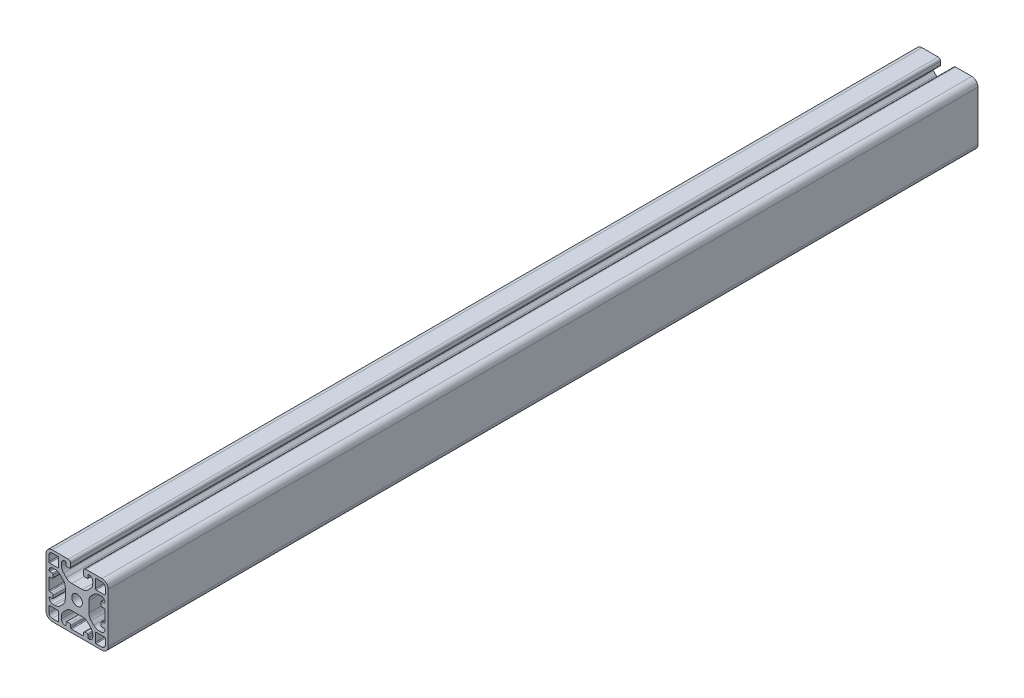
SolidWorks part; units mm, degrees
ref_plane "Ebene vorne" through (0, 0, 0) normal (0, 0, 1) x (1, 0, 0)
ref_plane "Ebene oben" through (0, 0, 0) normal (0, 1, 0) x (1, 0, 0)
ref_plane "Ebene rechts" through (0, 0, 0) normal (1, 0, 0) x (0, 0, -1)
ref_plane "Ebene1" through (0, 0, 560) normal (0, 0, 1) x (1, 0, 0)
sketch "Skizze1" plane through (0, 0, 560) normal (0, 0, 1) x (1, 0, 0)
  line L0 (0, 38.2) -> (3.7, 38.2)
  line L1 (4.2, 37.7) -> (4.2, 32.3)
  line L2 (3.7, 31.8) -> (-1.7, 31.8)
  line L3 (-2.2, 32.3) -> (-2.2, 36)
  line L4 (-2.2, 4) -> (-2.2, 7.7)
  line L5 (-1.7, 8.2) -> (3.7, 8.2)
  line L6 (4.2, 7.7) -> (4.2, 2.3)
  line L7 (3.7, 1.8) -> (0, 1.8)
  line L8 (32, 1.8) -> (28.3, 1.8)
  line L9 (27.8, 2.3) -> (27.8, 7.7)
  line L10 (28.3, 8.2) -> (33.7, 8.2)
  line L11 (34.2, 7.7) -> (34.2, 4)
  line L12 (34.2, 36) -> (34.2, 32.3)
  line L13 (33.7, 31.8) -> (28.3, 31.8)
  line L14 (27.8, 32.3) -> (27.8, 37.7)
  line L15 (28.3, 38.2) -> (32, 38.2)
  line L16 (12.5924, 12.4) -> (19.4076, 12.4)
  line L17 (22.9431, 10.9355) -> (24.6355, 9.2431)
  line L18 (26.1, 5.7076) -> (26.1, 4.5)
  line L19 (23.1, 2.5) -> (23.1, 4.15)
  line L20 (22.6, 4.65) -> (21.1, 4.65)
  line L21 (20.1, 3.65) -> (20.1, 2.5)
  line L22 (19.6, 2) -> (12.4, 2)
  line L23 (11.9, 2.5) -> (11.9, 3.65)
  line L24 (10.9, 4.65) -> (9.4, 4.65)
  line L25 (8.9, 4.15) -> (8.9, 2.5)
  line L26 (5.9, 4.5) -> (5.9, 5.7076)
  line L27 (7.3645, 9.2431) -> (9.0569, 10.9355)
  line L28 (-0.35, 15.9) -> (-1.5, 15.9)
  line L29 (-2, 16.4) -> (-2, 23.6)
  line L30 (-1.5, 24.1) -> (-0.35, 24.1)
  line L31 (0.65, 25.1) -> (0.65, 26.6)
  line L32 (0.15, 27.1) -> (-1.5, 27.1)
  line L33 (0.5, 30.1) -> (1.7076, 30.1)
  line L34 (5.2431, 28.6355) -> (6.9355, 26.9431)
  line L35 (8.4, 23.4076) -> (8.4, 16.5924)
  line L36 (6.9355, 13.0569) -> (5.2431, 11.3645)
  line L37 (1.7076, 9.9) -> (0.5, 9.9)
  line L38 (-1.5, 12.9) -> (0.15, 12.9)
  line L39 (0.65, 13.4) -> (0.65, 14.9)
  line L40 (23.6, 16.5924) -> (23.6, 23.4076)
  line L41 (25.0645, 26.9431) -> (26.7569, 28.6355)
  line L42 (30.2924, 30.1) -> (31.5, 30.1)
  line L43 (33.5, 27.1) -> (31.85, 27.1)
  line L44 (31.35, 26.6) -> (31.35, 25.1)
  line L45 (32.35, 24.1) -> (33.5, 24.1)
  line L46 (34, 23.6) -> (34, 16.4)
  line L47 (33.5, 15.9) -> (32.35, 15.9)
  line L48 (31.35, 14.9) -> (31.35, 13.4)
  line L49 (31.85, 12.9) -> (33.5, 12.9)
  line L50 (31.5, 9.9) -> (30.2924, 9.9)
  line L51 (26.7569, 11.3645) -> (25.0645, 13.0569)
  line L52 (23.1, 35.85) -> (23.1, 37.5)
  line L53 (26.1, 35.5) -> (26.1, 34.2924)
  line L54 (24.6355, 30.7569) -> (22.9431, 29.0645)
  line L55 (19.4076, 27.6) -> (12.5924, 27.6)
  line L56 (9.0569, 29.0645) -> (7.3645, 30.7569)
  line L57 (5.9, 34.2924) -> (5.9, 35.5)
  line L58 (8.9, 37.5) -> (8.9, 35.85)
  line L59 (9.4, 35.35) -> (10.9, 35.35)
  line L60 (11.9, 36.35) -> (11.9, 38.5)
  line L61 (10.4, 40) -> (0, 40)
  line L62 (-4, 36) -> (-4, 4)
  line L63 (0, 0) -> (32, 0)
  line L64 (36, 4) -> (36, 36)
  line L65 (32, 40) -> (21.6, 40)
  line L66 (20.1, 38.5) -> (20.1, 36.35)
  line L67 (21.1, 35.35) -> (22.6, 35.35)
  circle A0 centre (16, 20) radius 3.4
  arc A1 (3.7, 38.2) -> (4.2, 37.7) centre (3.7, 37.7) cw
  arc A2 (4.2, 32.3) -> (3.7, 31.8) centre (3.7, 32.3) cw
  arc A3 (-1.7, 31.8) -> (-2.2, 32.3) centre (-1.7, 32.3) cw
  arc A4 (-2.2, 36) -> (0, 38.2) centre (0, 36) cw
  arc A5 (-2.2, 7.7) -> (-1.7, 8.2) centre (-1.7, 7.7) cw
  arc A6 (3.7, 8.2) -> (4.2, 7.7) centre (3.7, 7.7) cw
  arc A7 (4.2, 2.3) -> (3.7, 1.8) centre (3.7, 2.3) cw
  arc A8 (0, 1.8) -> (-2.2, 4) centre (0, 4) cw
  arc A9 (28.3, 1.8) -> (27.8, 2.3) centre (28.3, 2.3) cw
  arc A10 (27.8, 7.7) -> (28.3, 8.2) centre (28.3, 7.7) cw
  arc A11 (33.7, 8.2) -> (34.2, 7.7) centre (33.7, 7.7) cw
  arc A12 (34.2, 4) -> (32, 1.8) centre (32, 4) cw
  arc A13 (34.2, 32.3) -> (33.7, 31.8) centre (33.7, 32.3) cw
  arc A14 (28.3, 31.8) -> (27.8, 32.3) centre (28.3, 32.3) cw
  arc A15 (27.8, 37.7) -> (28.3, 38.2) centre (28.3, 37.7) cw
  arc A16 (32, 38.2) -> (34.2, 36) centre (32, 36) cw
  arc A17 (19.4076, 12.4) -> (22.9431, 10.9355) centre (19.4076, 7.4) cw
  arc A18 (24.6355, 9.2431) -> (26.1, 5.7076) centre (21.1, 5.7076) cw
  arc A19 (26.1, 4.5) -> (23.6, 2) centre (23.6, 4.5) cw
  arc A20 (23.6, 2) -> (23.1, 2.5) centre (23.6, 2.5) cw
  arc A21 (23.1, 4.15) -> (22.6, 4.65) centre (22.6, 4.15) ccw
  arc A22 (21.1, 4.65) -> (20.1, 3.65) centre (21.1, 3.65) ccw
  arc A23 (20.1, 2.5) -> (19.6, 2) centre (19.6, 2.5) cw
  arc A24 (12.4, 2) -> (11.9, 2.5) centre (12.4, 2.5) cw
  arc A25 (11.9, 3.65) -> (10.9, 4.65) centre (10.9, 3.65) ccw
  arc A26 (9.4, 4.65) -> (8.9, 4.15) centre (9.4, 4.15) ccw
  arc A27 (8.9, 2.5) -> (8.4, 2) centre (8.4, 2.5) cw
  arc A28 (8.4, 2) -> (5.9, 4.5) centre (8.4, 4.5) cw
  arc A29 (5.9, 5.7076) -> (7.3645, 9.2431) centre (10.9, 5.7076) cw
  arc A30 (9.0569, 10.9355) -> (12.5924, 12.4) centre (12.5924, 7.4) cw
  arc A31 (-1.5, 15.9) -> (-2, 16.4) centre (-1.5, 16.4) cw
  arc A32 (-2, 23.6) -> (-1.5, 24.1) centre (-1.5, 23.6) cw
  arc A33 (-0.35, 24.1) -> (0.65, 25.1) centre (-0.35, 25.1) ccw
  arc A34 (0.65, 26.6) -> (0.15, 27.1) centre (0.15, 26.6) ccw
  arc A35 (-1.5, 27.1) -> (-2, 27.6) centre (-1.5, 27.6) cw
  arc A36 (-2, 27.6) -> (0.5, 30.1) centre (0.5, 27.6) cw
  arc A37 (1.7076, 30.1) -> (5.2431, 28.6355) centre (1.7076, 25.1) cw
  arc A38 (6.9355, 26.9431) -> (8.4, 23.4076) centre (3.4, 23.4076) cw
  arc A39 (8.4, 16.5924) -> (6.9355, 13.0569) centre (3.4, 16.5924) cw
  arc A40 (5.2431, 11.3645) -> (1.7076, 9.9) centre (1.7076, 14.9) cw
  arc A41 (0.5, 9.9) -> (-2, 12.4) centre (0.5, 12.4) cw
  arc A42 (-2, 12.4) -> (-1.5, 12.9) centre (-1.5, 12.4) cw
  arc A43 (0.15, 12.9) -> (0.65, 13.4) centre (0.15, 13.4) ccw
  arc A44 (0.65, 14.9) -> (-0.35, 15.9) centre (-0.35, 14.9) ccw
  arc A45 (23.6, 23.4076) -> (25.0645, 26.9431) centre (28.6, 23.4076) cw
  arc A46 (26.7569, 28.6355) -> (30.2924, 30.1) centre (30.2924, 25.1) cw
  arc A47 (31.5, 30.1) -> (34, 27.6) centre (31.5, 27.6) cw
  arc A48 (34, 27.6) -> (33.5, 27.1) centre (33.5, 27.6) cw
  arc A49 (31.85, 27.1) -> (31.35, 26.6) centre (31.85, 26.6) ccw
  arc A50 (31.35, 25.1) -> (32.35, 24.1) centre (32.35, 25.1) ccw
  arc A51 (33.5, 24.1) -> (34, 23.6) centre (33.5, 23.6) cw
  arc A52 (34, 16.4) -> (33.5, 15.9) centre (33.5, 16.4) cw
  arc A53 (32.35, 15.9) -> (31.35, 14.9) centre (32.35, 14.9) ccw
  arc A54 (31.35, 13.4) -> (31.85, 12.9) centre (31.85, 13.4) ccw
  arc A55 (33.5, 12.9) -> (34, 12.4) centre (33.5, 12.4) cw
  arc A56 (34, 12.4) -> (31.5, 9.9) centre (31.5, 12.4) cw
  arc A57 (30.2924, 9.9) -> (26.7569, 11.3645) centre (30.2924, 14.9) cw
  arc A58 (25.0645, 13.0569) -> (23.6, 16.5924) centre (28.6, 16.5924) cw
  arc A59 (22.6, 35.35) -> (23.1, 35.85) centre (22.6, 35.85) ccw
  arc A60 (23.1, 37.5) -> (23.6, 38) centre (23.6, 37.5) cw
  arc A61 (23.6, 38) -> (26.1, 35.5) centre (23.6, 35.5) cw
  arc A62 (26.1, 34.2924) -> (24.6355, 30.7569) centre (21.1, 34.2924) cw
  arc A63 (22.9431, 29.0645) -> (19.4076, 27.6) centre (19.4076, 32.6) cw
  arc A64 (12.5924, 27.6) -> (9.0569, 29.0645) centre (12.5924, 32.6) cw
  arc A65 (7.3645, 30.7569) -> (5.9, 34.2924) centre (10.9, 34.2924) cw
  arc A66 (5.9, 35.5) -> (8.4, 38) centre (8.4, 35.5) cw
  arc A67 (8.4, 38) -> (8.9, 37.5) centre (8.4, 37.5) cw
  arc A68 (8.9, 35.85) -> (9.4, 35.35) centre (9.4, 35.85) ccw
  arc A69 (10.9, 35.35) -> (11.9, 36.35) centre (10.9, 36.35) ccw
  arc A70 (11.9, 38.5) -> (10.4, 40) centre (10.4, 38.5) ccw
  arc A71 (0, 40) -> (-4, 36) centre (0, 36) ccw
  arc A72 (-4, 4) -> (0, 0) centre (0, 4) ccw
  arc A73 (32, 0) -> (36, 4) centre (32, 4) ccw
  arc A74 (36, 36) -> (32, 40) centre (32, 36) ccw
  arc A75 (21.6, 40) -> (20.1, 38.5) centre (21.6, 38.5) ccw
  arc A76 (20.1, 36.35) -> (21.1, 35.35) centre (21.1, 36.35) ccw
extrude "Aufsatz-Linear austragen1" add sketch "Skizze1" against normal blind 560
hole_wizard "M3 Gewindebohrung1" positions "Skizze2" profile "Skizze3" tap size "M3" standard "DIN" end condition through all
sketch "Skizze2" plane through (0, 0, 0) normal (0, -1, 0) x (-1, 0, 0)
  line L0 (-16, -560) -> (-16, -428.2078) construction
  line L1 (0, -560) -> (-32, -560) construction
  point P6 (-16, -500)
  dimension "D1" = 60
sketch "Skizze3" plane through (16, 0, 500) normal (1, 0, 0) x (0, 0, -1)
  line L0 (0, 0) -> (0, 27.6)
  line L1 (0, 27.6) -> (1.525, 27.6)
  line L2 (1.25, 27.325) -> (1.25, 0)
  line L5 (1.25, 0) -> (0, 0)
  line L7 (1.525, 27.6) -> (1.25, 27.325)
  line L8 (-1.525, 27.6) -> (-1.25, 27.325) construction
  line L11 (0, -6.35) -> (0, 107.95) construction
  dimension "Bohrerdurchmesser" = 2.5
  dimension "Bohrungstiefe" = 27.6
  dimension "Senkdurchmesser (Unten)" = 3.05
  dimension "Senkwinkel (Unten)" = 90
cosmetic thread "Bohrungsgewinde1" parameters "D2"=3
pattern_linear "Lineares Muster1" count 20 spacing 25 along (0, 0, -1) of "M3 Gewindebohrung1"
